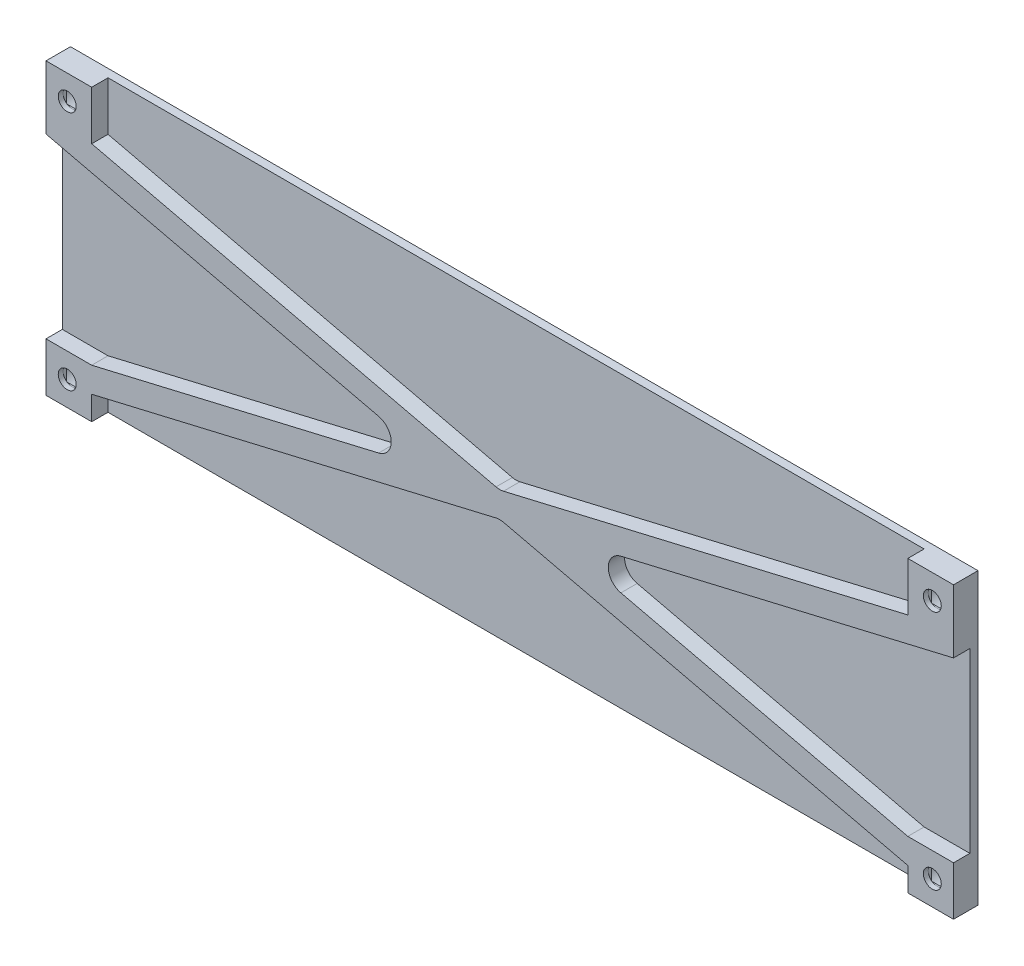
SolidWorks part; units mm, degrees
ref_plane "Front Plane" through (0, 0, 0) normal (0, 0, 1) x (1, 0, 0)
ref_plane "Top Plane" through (0, 0, 0) normal (0, 1, 0) x (1, 0, 0)
ref_plane "Right Plane" through (0, 0, 0) normal (1, 0, 0) x (0, 0, -1)
sketch "Sketch1" plane through (0, 0, 0) normal (0, 0, 1) x (1, 0, 0)
  line L1 (-56, -17.75) -> (56, -17.75)
  line L2 (-56, -17.75) -> (-56, 17.75)
  line L3 (-56, 17.75) -> (56, 17.75)
  line L4 (56, -17.75) -> (56, 17.75)
  line L5 (-56, -17.75) -> (56, 17.75) construction
  line L6 (-56, 17.75) -> (56, -17.75) construction
  point P0 (0, 0)
  dimension "D1" = 112
  dimension "D2" = 35.5
extrude "Boss-Extrude1" add sketch "Sketch1" along normal blind 1
sketch "Sketch2" plane through (0, 0, 1) normal (0, 0, 1) x (1, 0, 0)
  line L0 (0, -17.75) -> (0, 17.75) construction
  line L1 (-56, 17.75) -> (-50, 17.75)
  line L2 (-56, 17.75) -> (-56, 11.75)
  line L3 (-56, 11.75) -> (-50, 11.75)
  line L4 (-50, 17.75) -> (-50, 11.75)
  line L5 (-56, -17.75) -> (56, -17.75) construction
  line L6 (56, 17.75) -> (-56, 17.75) construction
  line L7 (-56, 0) -> (56, 0) construction
  line L8 (-56, 17.75) -> (-56, -17.75) construction
  line L9 (56, -17.75) -> (56, 17.75) construction
  line L10 (-50, -17.75) -> (-50, -11.75)
  line L11 (-56, -11.75) -> (-50, -11.75)
  line L12 (-56, -17.75) -> (-56, -11.75)
  line L13 (-56, -17.75) -> (-50, -17.75)
  line L14 (56, -17.75) -> (50, -17.75)
  line L15 (56, -17.75) -> (56, -11.75)
  line L16 (56, -11.75) -> (50, -11.75)
  line L17 (50, -17.75) -> (50, -11.75)
  line L18 (50, 17.75) -> (50, 11.75)
  line L19 (56, 11.75) -> (50, 11.75)
  line L20 (56, 17.75) -> (56, 11.75)
  line L21 (56, 17.75) -> (50, 17.75)
  dimension "D1" = 6
extrude "Boss-Extrude2" add sketch "Sketch2" along normal blind 2
sketch "Sketch3" plane through (0, 0, 3) normal (0, 0, 1) x (1, 0, 0)
  line L0 (-56, 0) -> (56, 0) construction
  line L1 (-56, 11.75) -> (-56, -11.75) construction
  line L2 (56, -11.75) -> (56, 11.75) construction
  line L3 (0, 17.75) -> (0, -17.75) construction
  line L4 (50, 17.75) -> (-50, 17.75) construction
  line L5 (-50, -17.75) -> (50, -17.75) construction
  line L6 (-56, 11.75) -> (-50, 17.75) construction
  line L7 (-56, -11.75) -> (-50, -17.75) construction
  line L8 (56, -11.75) -> (50, -17.75) construction
  line L9 (56, 11.75) -> (50, 17.75) construction
  circle A0 centre (-53, 14.75) radius 1.1
  circle A1 centre (-53, -14.75) radius 1.1
  circle A2 centre (53, -14.75) radius 1.1
  circle A3 centre (53, 14.75) radius 1.1
  dimension "D1" = 2.2
extrude "Cut-Extrude1" cut sketch "Sketch3" against normal through all
sketch "Sketch4" plane through (0, 0, 0) normal (0, 0, -1) x (-1, 0, 0)
  circle A0 centre (-53, 14.75) radius 2
  circle A1 centre (-53, -14.75) radius 2
  circle A2 centre (53, 14.75) radius 2
  circle A3 centre (53, -14.75) radius 2
  dimension "D1" = 4
extrude "Cut-Extrude2" cut sketch "Sketch4" against normal blind 2
sketch "Sketch5" plane through (0, 0, 2) normal (0, 0, -1) x (-1, 0, 0)
  line L2 (-54.1, 13.0797) -> (-54.1, 16.4203)
  line L4 (-51.9, 13.0797) -> (-51.9, 16.4203)
  line L5 (-54.1, 13.0797) -> (-51.9, 16.4203) construction
  line L6 (-54.1, 16.4203) -> (-51.9, 13.0797) construction
  circle A0 centre (-53, 14.75) radius 2 construction
  circle A1 centre (-53, 14.75) radius 1.1 construction
  circle A2 centre (-53, 14.75) radius 2 construction
  arc A3 (-51.9, 16.4203) -> (-54.1, 16.4203) centre (-53, 14.75) ccw
  arc A4 (-54.1, 13.0797) -> (-51.9, 13.0797) centre (-53, 14.75) ccw
  point P0 (-53, 14.75)
extrude "Cut-Extrude3" cut sketch "Sketch5" against normal blind 0.2
sketch "Sketch6" plane through (0, 0, 2.2) normal (0, 0, -1) x (-1, 0, 0)
  line L0 (-51.9, 13.0797) -> (-51.9, 16.4203) construction
  line L1 (-54.1, 13.65) -> (-51.9, 13.65)
  line L2 (-54.1, 13.65) -> (-54.1, 15.85)
  line L3 (-54.1, 15.85) -> (-51.9, 15.85)
  line L4 (-51.9, 13.65) -> (-51.9, 15.85)
  line L5 (-54.1, 13.65) -> (-51.9, 15.85) construction
  line L6 (-54.1, 15.85) -> (-51.9, 13.65) construction
  arc A0 (-51.9, 14.75) -> (-54.1, 14.75) centre (-53, 14.75) ccw construction
  point P0 (-53, 14.75)
extrude "Cut-Extrude4" cut sketch "Sketch6" against normal blind 0.2
mirror "Mirror1" about plane through (0, 0, 0) normal (1, 0, 0) of "Cut-Extrude4", "Cut-Extrude3"
mirror "Mirror2" about plane through (0, 0, 0) normal (0, 1, 0) of "Mirror1", "Cut-Extrude3", "Cut-Extrude4"
sketch "Sketch7" plane through (0, 0, 0) normal (0, 0, -1) x (-1, 0, 0)
  line L0 (56, -17.75) -> (-56, -17.75) construction
  line L1 (-56, 17.75) -> (-55.6, 17.75)
  line L2 (-56, 17.75) -> (-56, -17.75)
  line L3 (-56, -17.75) -> (-55.6, -17.75)
  line L4 (-55.6, 17.75) -> (-55.6, -17.75)
  line L6 (56, 17.75) -> (55.6, 17.75)
  line L7 (56, 17.75) -> (56, -17.75)
  line L8 (56, -17.75) -> (55.6, -17.75)
  line L9 (55.6, 17.75) -> (55.6, -17.75)
  dimension "D1" = 0.4
extrude "Cut-Extrude5" cut sketch "Sketch7" against normal through all
sketch "Skizze5" plane through (0, 0, 1) normal (0, 0, 1) x (1, 0, 0)
  line L0 (-50, 11.75) -> (0, 0)
  line L1 (50, 11.75) -> (0, 0)
  line L2 (-55.6, 9.9843) -> (-6.5569, -1.5409)
  line L3 (-50, -11.75) -> (-50, -14.8317)
  line L4 (50, -14.8317) -> (50, -11.75)
  line L5 (-55.6, 11.75) -> (-55.6, -11.75) construction
  line L7 (-50, -14.8317) -> (0, -3.0817)
  line L8 (55.6, -11.75) -> (55.6, 11.75) construction
  line L9 (-55.6, 9.9843) -> (-55.6, 11.75)
  line L10 (-55.6, 11.75) -> (-50, 11.75)
  line L11 (50, 11.75) -> (55.6, 11.75)
  line L12 (55.6, 11.75) -> (55.6, 9.9843)
  line L13 (6.5569, -1.5409) -> (50, -11.75)
  line L14 (0, -3.0817) -> (50, -14.8317)
  line L15 (-6.5569, -1.5409) -> (-50, -11.75)
  line L16 (6.5569, -1.5409) -> (55.6, 9.9843)
  dimension "D1" = 3
  dimension "D2" = 3
extrude "Aufsatz-Linear austragen2" add sketch "Skizze5" along normal up to surface (2 mm away) up to face at (-52.8, 14.75, 3)
fillet "Verrundung1" radius 2 4 edges at (0, -3.0817, 2) (0, 0, 2) (-6.5569, -1.5409, 2) (6.5569, -1.5409, 2)
sketch "Skizze15" plane through (0, 0, 0) normal (0, 0, 1) x (1, 0, 0)
  line L0 (14.2986, 11.3636) -> (21.9557, 11.3636)
  line L1 (31.6412, 6.8567) -> (32.7999, -5.1663)
  line L2 (25.8346, -12.6051) -> (23.6181, 10.4031)
  line L3 (27.2216, 14.4735) -> (46.2166, 14.4701)
  line L4 (34.7746, -9.4919) -> (33.3507, 5.2917)
  line L5 (33.3507, 5.2917) -> (41.0212, 5.3085)
  line L6 (42.4519, -9.4751) -> (34.7746, -9.4919)
  spline S0 degree 3 poles (24.2696, -12.6119) (22.1605, -12.6119) (20.6459, -11.9872) (19.4705, -11.198) knots 0 0 0 0 1 1 1 1
  spline S1 degree 3 poles (19.4705, -11.198) (18.3723, -10.4625) (17.5226, -9.5927) (16.8711, -8.471) knots 0 0 0 0 1 1 1 1
  spline S2 degree 3 poles (16.8711, -8.471) (16.0281, -7.0202) (15.9375, -5.6735) (15.8669, -4.8909) knots 0 0 0 0 1 1 1 1
  spline S3 degree 2 poles (15.8669, -4.8909) (15.8669, -4.8842) (14.2986, 11.3636) knots 0 0 0 1 1 1
  spline S4 degree 3 poles (21.9557, 11.3636) (21.959, 11.3636) (24.273, -12.6119) (24.2696, -12.6119) knots 0 0 0 0 1 1 1 1
  spline S5 degree 3 poles (32.7999, -5.1663) (32.9947, -7.7959) (32.0073, -9.146) (31.3961, -9.858) knots 0 0 0 0 1 1 1 1
  spline S6 degree 3 poles (31.3961, -9.858) (30.2744, -11.1577) (28.2157, -12.1786) (25.8346, -12.6051) knots 0 0 0 0 1 1 1 1
  spline S7 degree 3 poles (23.6181, 10.4031) (23.5475, 11.4946) (23.8632, 12.4484) (24.592, 13.2812) knots 0 0 0 0 1 1 1 1
  spline S8 degree 3 poles (24.592, 13.2812) (25.4417, 14.2518) (26.7011, 14.4735) (27.2216, 14.4735) knots 0 0 0 0 1 1 1 1
  spline S9 degree 3 poles (46.2166, 14.4701) (47.6204, 14.4701) (49.7295, 13.11) (49.7295, 10.7591) knots 0 0 0 0 1 1 1 1
  spline S10 degree 3 poles (49.7295, 10.7591) (49.7295, 7.8541) (47.1469, 6.8567) (46.2569, 6.8567) knots 0 0 0 0 1 1 1 1
  spline S11 degree 2 poles (46.2569, 6.8567) (45.8035, 6.8533) (31.6412, 6.8567) knots 0 0 0 1 1 1
  spline S12 degree 2 poles (41.0212, 5.3085) (42.2705, -7.5609) (42.4519, -9.4751) knots 0 0 0 1 1 1
